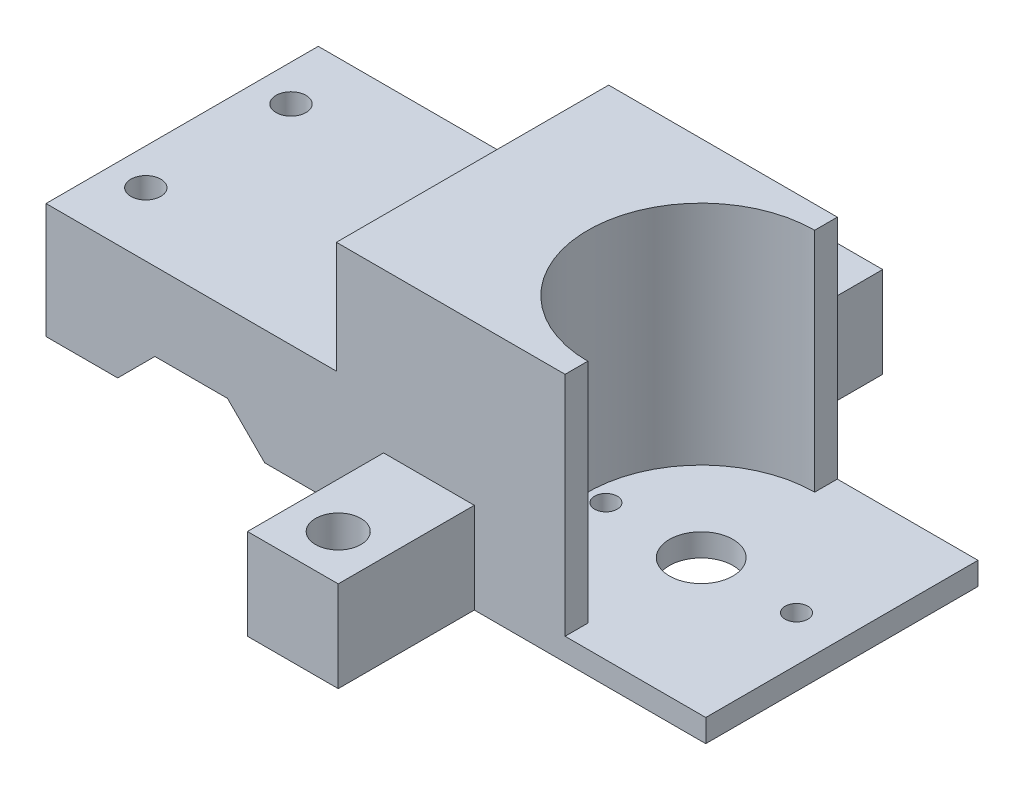
SolidWorks part; units mm, degrees
ref_plane "Front Plane" through (0, 0, 0) normal (0, 0, 1) x (1, 0, 0)
ref_plane "Top Plane" through (0, 0, 0) normal (0, 1, 0) x (1, 0, 0)
ref_plane "Right Plane" through (0, 0, 0) normal (1, 0, 0) x (0, 0, -1)
sketch "Sketch1" plane through (0, 0, 0) normal (0, 0, 1) x (1, 0, 0)
  line L0 (0, 12.1598) -> (0, -9.8313) construction
  line L1 (-4, 4.1012) -> (4, 4.1012)
  line L2 (4, 4.1012) -> (8.1012, 0)
  line L3 (8.1012, 0) -> (16, 0)
  line L4 (16, 0) -> (16, 12.7)
  line L5 (16, 12.7) -> (-16, 12.7)
  line L6 (-16, 0) -> (-16, 12.7)
  line L7 (-8.1012, 0) -> (-16, 0)
  line L8 (-4, 4.1012) -> (-8.1012, 0)
  line L11 (-16, 0) -> (-16, 12.7)
  point P3 (-12, 0)
  point P5 (12, 0)
  point P12 (0, 12.7)
  point P15 (0, 4.1012)
  dimension "D1" = 4
  dimension "D2" = 12
  dimension "D3" = 45
  dimension "D4" = 5.8
  dimension "D5" = 16
  dimension "D6" = 12.7
extrude "Boss-Extrude1" add sketch "Sketch1" along normal mid plane 30
sketch "Sketch2" plane through (0, 12.7, 0) normal (0, 1, 0) x (1, 0, 0)
  line L2 (16, 0) -> (-16, 0) construction
  circle A0 centre (12, 8) radius 1.65
  circle A1 centre (12, -8) radius 1.65
  circle A2 centre (-12, -8) radius 1.65
  circle A3 centre (-12, 8) radius 1.65
  dimension "D1" = 3.3
  dimension "D2" = 16
  dimension "D3" = 8
extrude "Cut-Extrude1" cut sketch "Sketch2" against normal up to surface (12.7 mm away) up to face at (-12.0506, 0, 0)
sketch "Sketch12" plane through (16, 0, 0) normal (1, 0, 0) x (0, 0, -1)
  line L0 (-15, 0) -> (-15, 12.7) construction
  line L1 (15, 0) -> (-15, 0)
  line L2 (15, 0) -> (15, 25)
  line L3 (15, 25) -> (-15, 25)
  line L4 (-15, 0) -> (-15, 25)
  dimension "D1" = 25
extrude "Boss-Extrude9" add sketch "Sketch12" along normal blind 25.2
sketch "Sketch13" plane through (0, 25, 0) normal (0, 1, 0) x (1, 0, 0)
  line L0 (16, 15) -> (16, -15) construction
  line L1 (-55, 0) -> (55, 0) construction
  line L2 (41.2, 12.5) -> (41.2, -12.5)
  arc A0 (41.2, 12.5) -> (41.2, -12.5) centre (41.2, 0) ccw
  point P2 (28.7, 0)
  dimension "D1" = 25
  dimension "D2" = 12.7
extrude "Cut-Extrude2" cut sketch "Sketch13" against normal up to surface (25 mm away) up to face at (13.65, 0, 8)
sketch "Sketch14" plane through (0, 0, 0) normal (0, -1, 0) x (1, 0, 0)
  line L1 (21.2, -15) -> (56.7, -15)
  line L2 (21.2, -15) -> (21.2, 15)
  line L3 (21.2, 15) -> (56.7, 15)
  line L4 (56.7, -15) -> (56.7, 15)
  line L5 (8.1012, 15) -> (41.2, 15) construction
  line L6 (8.1012, -15) -> (41.2, -15) construction
  circle A0 centre (41.2, 0) radius 3.5
  circle A1 centre (51.7, 0) radius 1.25
  circle A2 centre (30.7, 0) radius 1.25
  arc A3 (41.2, 12.5) -> (41.2, -12.5) centre (41.2, 0) ccw construction
  dimension "D1" = 7
  dimension "D4" = 2.5
  dimension "D2" = 21
  dimension "D3" = 10.5
  dimension "D5" = 5
  dimension "D6" = 20
extrude "Boss-Extrude10" add sketch "Sketch14" along normal blind 2.5
sketch "Sketch15" plane through (0, -2.5, 0) normal (0, -1, 0) x (1, 0, 0)
  line L0 (8.1012, 15) -> (21.2, 15) construction
  line L1 (31.2, 30) -> (21.2, 30)
  line L2 (31.2, 30) -> (31.2, 15)
  line L3 (31.2, 15) -> (21.2, 15)
  line L4 (21.2, 30) -> (21.2, 15)
  line L5 (8.1012, -15) -> (21.2, -15) construction
  line L6 (21.2, -15) -> (31.2, -15)
  line L7 (21.2, -15) -> (21.2, -30)
  line L8 (21.2, -30) -> (31.2, -30)
  line L9 (31.2, -15) -> (31.2, -30)
  line L10 (21.2, 15) -> (21.2, -15) construction
  circle A0 centre (26.2, 25) radius 2.5
  circle A1 centre (26.2, -25) radius 2.5
  circle A2 centre (41.2, 0) radius 3.5 construction
  dimension "D1" = 5
  dimension "D2" = 15
  dimension "D3" = 15
  dimension "D4" = 5
  dimension "D5" = 5
  dimension "D6" = 5
extrude "Boss-Extrude11" add sketch "Sketch15" against normal blind 10
